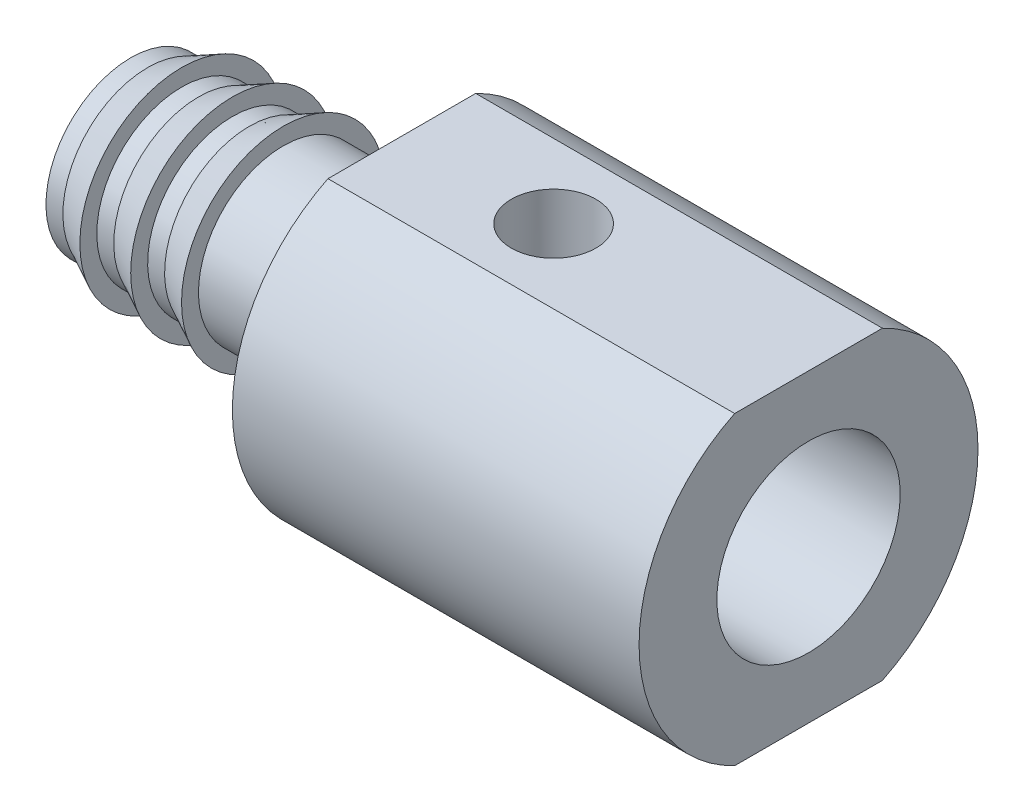
SolidWorks part; units mm, degrees
ref_plane "Front Plane" through (0, 0, 0) normal (0, 0, 1) x (1, 0, 0)
ref_plane "Top Plane" through (0, 0, 0) normal (0, 1, 0) x (1, 0, 0)
ref_plane "Right Plane" through (0, 0, 0) normal (1, 0, 0) x (0, 0, -1)
sketch "Sketch1" plane through (0, 0, 0) normal (0, 0, 1) x (1, 0, 0)
  line L0 (2.2716, -7.7593) -> (-7.2343, -7.7593) construction
  line L7 (-1.3159, -5.2593) -> (-4.8159, -5.2593)
  line L16 (-9.3159, -5.7593) -> (0.6841, -5.7593)
  line L23 (-9.3159, -5.7593) -> (-9.3159, -5.2593)
  line L35 (-8.8159, -5.2593) -> (-7.8159, -4.7593)
  line L36 (-7.8159, -4.7593) -> (-7.8159, -5.2593)
  line L37 (-8.8159, -5.2593) -> (-9.3159, -5.2593)
  line L38 (-7.3159, -5.2593) -> (-6.3159, -4.7593)
  line L39 (-6.3159, -4.7593) -> (-6.3159, -5.2593)
  line L40 (-5.8159, -5.2593) -> (-4.8159, -4.7593)
  line L41 (-4.8159, -4.7593) -> (-4.8159, -5.2593)
  line L42 (-7.3159, -5.2593) -> (-7.8159, -5.2593)
  line L43 (-5.8159, -5.2593) -> (-6.3159, -5.2593)
  line L45 (-1.3159, -5.2593) -> (-1.3159, -2.7593)
  line L46 (-1.3159, -2.7593) -> (10.6841, -2.7593)
  line L48 (10.6841, -2.7593) -> (10.6841, -7.7593)
  line L49 (10.6841, -7.7593) -> (0.6841, -7.7593)
  line L50 (0.6841, -5.7593) -> (0.6841, -7.7593)
  dimension "D2" = 10
  dimension "D3" = 2
  dimension "D4" = 2.5
  dimension "D5" = 5
  dimension "D6" = 0.5
  dimension "D7" = 10
  dimension "D14" = 3
  dimension "D15" = 1
  dimension "D16" = 1
  dimension "D17" = 1
  dimension "D18" = 0.5
  dimension "D19" = 1.5
  dimension "D20" = 1.5
revolve "Revolve1" add sketch "Sketch1" angle 360 about L0
sketch "Sketch4" plane through (10.6841, 0, 0) normal (1, 0, 0) x (0, 0, -1)
  line L1 (-16, -3.2593) -> (16, -3.2593)
  line L2 (-16, -3.2593) -> (-16, -12.2593)
  line L3 (-16, -12.2593) -> (16, -12.2593)
  line L4 (16, -3.2593) -> (16, -12.2593)
  point P4 (0, -7.7593)
  dimension "D1" = 9
  dimension "D2" = 4.5
  dimension "D3" = 32
  dimension "D4" = 16
extrude "Cut-Extrude1" cut sketch "Sketch4" against normal through all flip side to cut contours L1 L4 L3 L2
hole_wizard "1/4-28 Tapped Hole2" positions "Sketch10" profile "Sketch11" tap size "1/4-28" standard "ANSI Inch" end condition up to next
sketch "Sketch10" plane through (10.6841, 0, 0) normal (1, 0, 0) x (0, 0, -1)
  point P0 (0, -7.7593)
sketch "Sketch11" plane through (10.6841, -7.7593, 0) normal (0, 1, 0) x (0, 0, -1)
  line L0 (0, 0) -> (0, 10)
  line L1 (0, 10) -> (2.7051, 10)
  line L2 (2.7051, 10) -> (2.7051, 0)
  line L5 (2.7051, 0) -> (0, 0)
  line L11 (0, -6.35) -> (0, 107.95) construction
  dimension "Thru Tap Drill Dia." = 5.4102
  dimension "Thru Tap Drill Depth" = 10
cosmetic thread "Hole Thread2" parameters "D2"=6.35
hole_wizard "M3 Tapped Hole1" positions "Sketch12" profile "Sketch13" tap size "M3" standard "ISO" end condition through all
sketch "Sketch12" plane through (0, -3.2593, 0) normal (0, 1, 0) x (1, 0, 0)
  point P0 (3.1624, 0)
sketch "Sketch13" plane through (3.1624, -3.2593, 0) normal (1, 0, 0) x (0, 0, 1)
  line L0 (0, 0) -> (0, 9)
  line L1 (0, 9) -> (1.25, 9)
  line L2 (1.25, 9) -> (1.25, 0)
  line L5 (1.25, 0) -> (0, 0)
  line L11 (0, -6.35) -> (0, 107.95) construction
  dimension "Thru Tap Drill Dia." = 2.5
  dimension "Thru Tap Drill Depth" = 9
cosmetic thread "Hole Thread3" parameters "D2"=3
equation "\"D2@Sketch4\"=\"D1@Sketch4\"/2"
